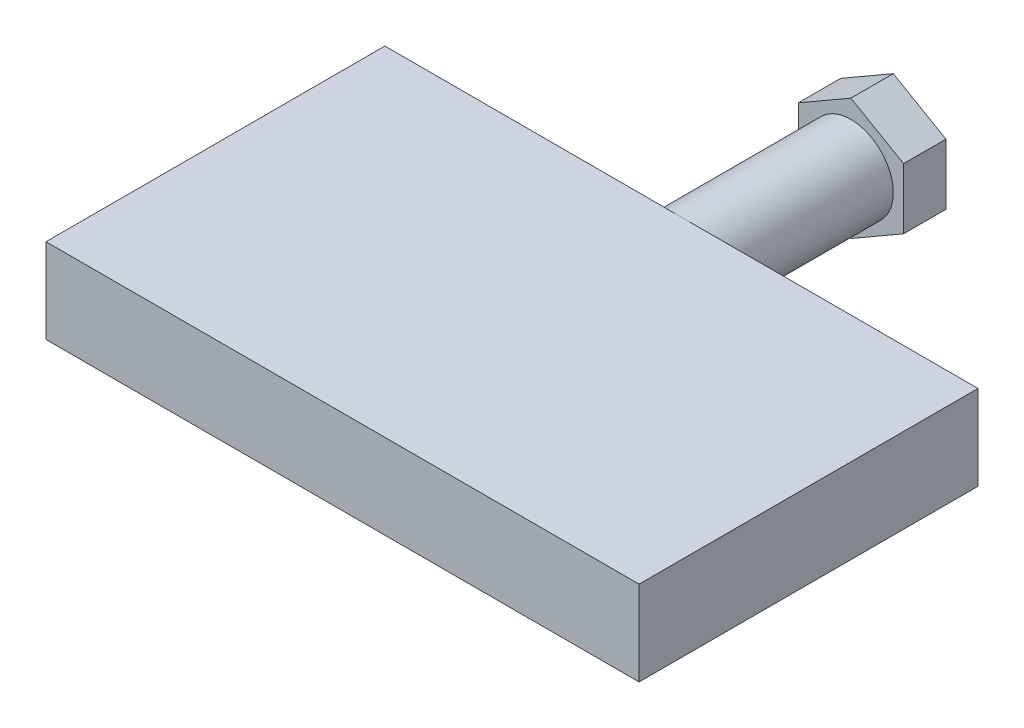
SolidWorks part; units mm, degrees
ref_plane "Front Plane" through (0, 0, 0) normal (0, 0, 1) x (1, 0, 0)
ref_plane "Top Plane" through (0, 0, 0) normal (0, 1, 0) x (1, 0, 0)
ref_plane "Right Plane" through (0, 0, 0) normal (1, 0, 0) x (0, 0, -1)
sketch "Sketch1" plane through (0, 0, 0) normal (0, 1, 0) x (1, 0, 0)
  line L0 (0, 0) -> (0, 0.6576)
  line L1 (0, 40.6576) -> (35, 40.6576)
  line L2 (35, 40.6576) -> (35, 0.6576)
  line L3 (35, 0.6576) -> (-35, 0.6576)
  line L4 (-35, 0.6576) -> (-35, 40.6576)
  line L5 (-35, 40.6576) -> (0, 40.6576)
  dimension "D1" = 35
  dimension "D2" = 40
  dimension "D3" = 35
extrude "Boss-Extrude1" add sketch "Sketch1" along normal blind 10 contours L5 L4 L3 L2 L1
sketch "Sketch2" plane through (0, 0, -40.6576) normal (0, 0, -1) x (-1, 0, 0)
  circle A1 centre (0, 5) radius 5
extrude "Boss-Extrude2" add sketch "Sketch2" along normal blind 20
sketch "Sketch3" plane through (0, 0, -60.6576) normal (0, 0, -1) x (-1, 0, 0)
  line L7 (0, -2.1761) -> (6.2147, 1.4119)
  line L8 (6.2147, 1.4119) -> (6.2147, 8.5881)
  line L9 (6.2147, 8.5881) -> (0, 12.1761)
  line L10 (0, 12.1761) -> (-6.2147, 8.5881)
  line L11 (-6.2147, 8.5881) -> (-6.2147, 1.4119)
  line L12 (-6.2147, 1.4119) -> (0, -2.1761)
  circle A0 centre (0, 5) radius 6.2147 construction
extrude "Boss-Extrude4" add sketch "Sketch3" along normal blind 5
